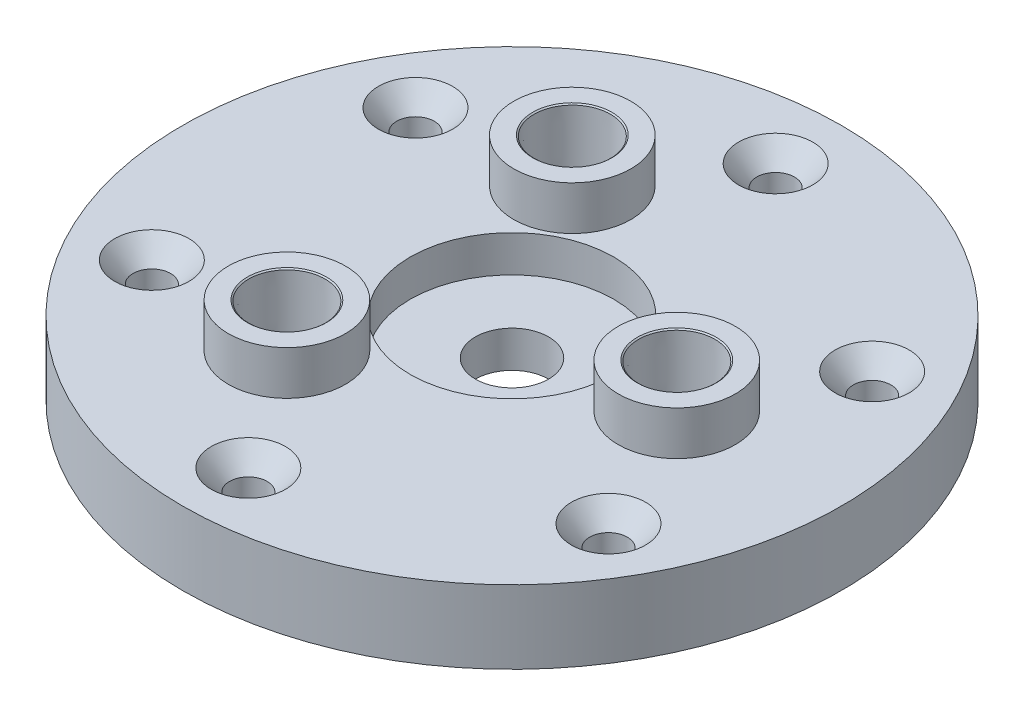
SolidWorks part; units mm, degrees
ref_plane "Front Plane" through (0, 0, 0) normal (0, 0, 1) x (1, 0, 0)
ref_plane "Top Plane" through (0, 0, 0) normal (0, 1, 0) x (1, 0, 0)
ref_plane "Right Plane" through (0, 0, 0) normal (1, 0, 0) x (0, 0, -1)
sketch "Sketch1" plane through (0, 0, 0) normal (0, 1, 0) x (1, 0, 0)
  circle A0 centre (0, 0) radius 57.15
  dimension "D1" = 114.3
extrude "Boss-Extrude1" add sketch "Sketch1" along normal blind 6.35
sketch "Sketch2" plane through (0, 6.35, 0) normal (0, 1, 0) x (1, 0, 0)
  circle A0 centre (0, 0) radius 6.35
  dimension "D1" = 12.7
extrude "Cut-Extrude1" cut sketch "Sketch2" against normal through all both and the other way through all
sketch "Sketch3" plane through (0, 6.35, 0) normal (0, 1, 0) x (1, 0, 0)
  circle A0 centre (0, 0) radius 57.15
  circle A1 centre (0, 0) radius 57.15 construction
  circle A2 centre (0, 0) radius 17.653
  dimension "D1" = 35.306
extrude "Boss-Extrude2" add sketch "Sketch3" along normal blind 6.35
sketch "Annulus Entrance" plane through (0, 12.7, 0) normal (0, 1, 0) x (1, 0, 0)
  line L0 (0, 0) -> (57.15, 0) construction
  line L1 (0, 0) -> (-28.575, -49.4934) construction
  line L2 (0, 0) -> (-28.575, 49.4934) construction
  circle A0 centre (0, 0) radius 57.15 construction
  circle A1 centre (28.575, 0) radius 3.175
  circle A2 centre (-14.2875, -24.7467) radius 3.175
  circle A3 centre (-14.2875, 24.7467) radius 3.175
  circle A4 centre (0, 0) radius 28.575 construction
  point P17 (0, 0)
  dimension "D1" = 6.35
  dimension "D2" = 57.15
  dimension "D3" = 3
extrude "Cut-Extrude2" cut sketch "Annulus Entrance" against normal through all both and the other way through all
hole_wizard "CSK for 1/4 Flat Head Machine Screw1" positions "3DSketch1" profile "Sketch6" countersink size "1/4" standard "ANSI Inch" end condition through all
sketch3d "3DSketch1"
  line L3 (0, 12.7, 0) -> (0, 12.7, -45.72) construction
  line L4 (0, 12.7, 0) -> (0, 6.35, 0) construction
  point P0 (0, 12.7, -45.72)
  dimension "D1" = 45.72
sketch "Sketch6" plane through (0, 12.7, -45.72) normal (1, 0, 0) x (0, 0, 1)
  line L0 (0, 0) -> (0, 12.7)
  line L1 (0, 12.7) -> (3.2639, 12.7)
  line L2 (3.2639, 12.7) -> (3.2639, 3.6524)
  line L3 (3.2639, 3.6524) -> (6.4389, 0)
  line L5 (6.4389, 0) -> (0, 0)
  line L6 (-3.2639, 3.6524) -> (-6.4389, 0) construction
  line L11 (0, -6.35) -> (0, 107.95) construction
  dimension "Thru Hole Dia." = 6.5278
  dimension "Thru Hole Depth" = 12.7
  dimension "Near C'Sink Dia." = 12.8778
  dimension "Near C'Sink Angle" = 82
sketch "Sketch8" plane through (0, 12.7, 0) normal (0, 1, 0) x (1, 0, 0)
  circle A0 centre (0, 0) radius 35.7188 construction
  circle A2 centre (0, 0) radius 38.1 construction
  dimension "D1" = 76.2
  dimension "D2" = 71.4375
pattern_circular "CirPattern1" count 6 over 360 about axis through (0, 0, 0) along (0, 1, 0) of "CSK for 1/4 Flat Head Machine Screw1"
sketch "Sketch11" plane through (0, 12.7, 0) normal (0, 1, 0) x (1, 0, 0)
  circle A0 centre (-14.2875, 24.7467) radius 3.175
  circle A1 centre (28.575, 0) radius 3.175
  circle A2 centre (-14.2875, -24.7467) radius 3.175
  circle A4 centre (-14.2875, 24.7467) radius 3.175 construction
  circle A5 centre (28.575, 0) radius 3.175 construction
  circle A6 centre (-14.2875, -24.7467) radius 3.175 construction
  circle A7 centre (-14.2875, 24.7467) radius 10.16
  circle A8 centre (28.575, 0) radius 10.16
  circle A9 centre (-14.2875, -24.7467) radius 10.16
  dimension "D1" = 20.32
extrude "Boss-Extrude3" add sketch "Sketch11" along normal blind 7.62
hole_wizard "1/4 NPT Tapped Hole3" positions "Sketch12" profile "Sketch13" size "1/4" standard "ANSI Inch"
sketch "Sketch12" plane through (0, 20.32, 0) normal (0, 1, 0) x (1, 0, 0)
  point P0 (-14.2875, 24.7467)
  point P3 (28.575, 0)
  point P6 (-14.2875, -24.7467)
sketch "Sketch13" plane through (-14.2875, 20.32, -24.7467) normal (1, 0, 0) x (0, 0, 1)
  line L0 (0, 0) -> (0, 20.4111)
  line L1 (5.5626, 17.0688) -> (0, 20.4111)
  line L2 (-5.5626, 17.0688) -> (0, 20.4111) construction
  line L3 (5.5626, 17.0688) -> (5.5626, 10.0203)
  line L4 (5.5626, 10.0203) -> (6.3356, 10.0203)
  line L5 (6.3356, 10.0203) -> (6.6298, 0.1914)
  line L6 (6.6298, 0.1914) -> (6.858, 0)
  line L7 (6.858, 0) -> (0, 0)
  line L8 (0, -6.35) -> (0, 107.95) construction
  line L9 (-6.6298, 0.1914) -> (-6.858, 0) construction
  line L11 (-5.5626, 10.0203) -> (-6.3356, 10.0203) construction
  line L12 (-6.3356, 10.0203) -> (-6.6298, 0.1914) construction
  dimension "Tap Drill Dia." = 11.1252
  dimension "Tap Drill Depth" = 17.0688
  dimension "Thread Dia." = 13.2597
  dimension "Thread Angle" = 3.43
  dimension "Thread Depth" = 10.0203
  dimension "C'Sink Dia." = 13.716
  dimension "C'Sink Angle" = 100
  dimension "Drill Angle" = 118
